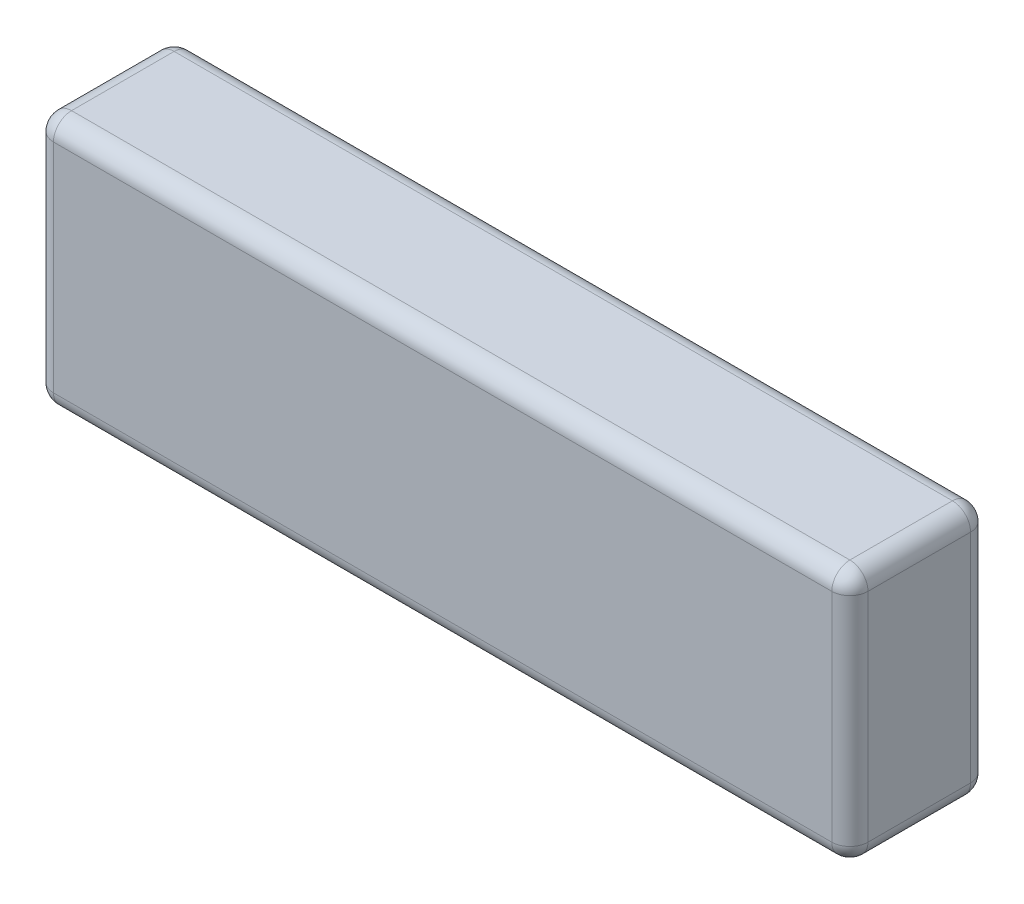
SolidWorks part; units mm, degrees
material "Plástico personalizado"
ref_plane "Plano frontal" through (0, 0, 0) normal (0, 0, 1) x (1, 0, 0)
ref_plane "Plano superior" through (0, 0, 0) normal (0, 1, 0) x (1, 0, 0)
ref_plane "Plano direito" through (0, 0, 0) normal (1, 0, 0) x (0, 0, -1)
sketch "Esboço1" plane through (0, 0, 0) normal (0, 0, 1) x (1, 0, 0)
  line L1 (-67.5, -21) -> (67.5, -21)
  line L2 (-67.5, -21) -> (-67.5, 21)
  line L3 (-67.5, 21) -> (67.5, 21)
  line L4 (67.5, -21) -> (67.5, 21)
  line L5 (-67.5, -21) -> (67.5, 21) construction
  line L6 (-67.5, 21) -> (67.5, -21) construction
  point P0 (0, 0)
  dimension "D1" = 135
  dimension "D2" = 42
extrude "Ressalto-extrusão1" add sketch "Esboço1" along normal mid plane 23
fillet "Filete1" radius 3 12 edges at (0, -21, 11.5) (0, 21, -11.5) (0, 21, 11.5) (67.5, 21, 0) (67.5, 0, -11.5) (67.5, -21, 0) (67.5, 0, 11.5) (-67.5, 0, 11.5) (-67.5, 21, 0) (-67.5, 0, -11.5) (-67.5, -21, 0) (0, -21, -11.5)
